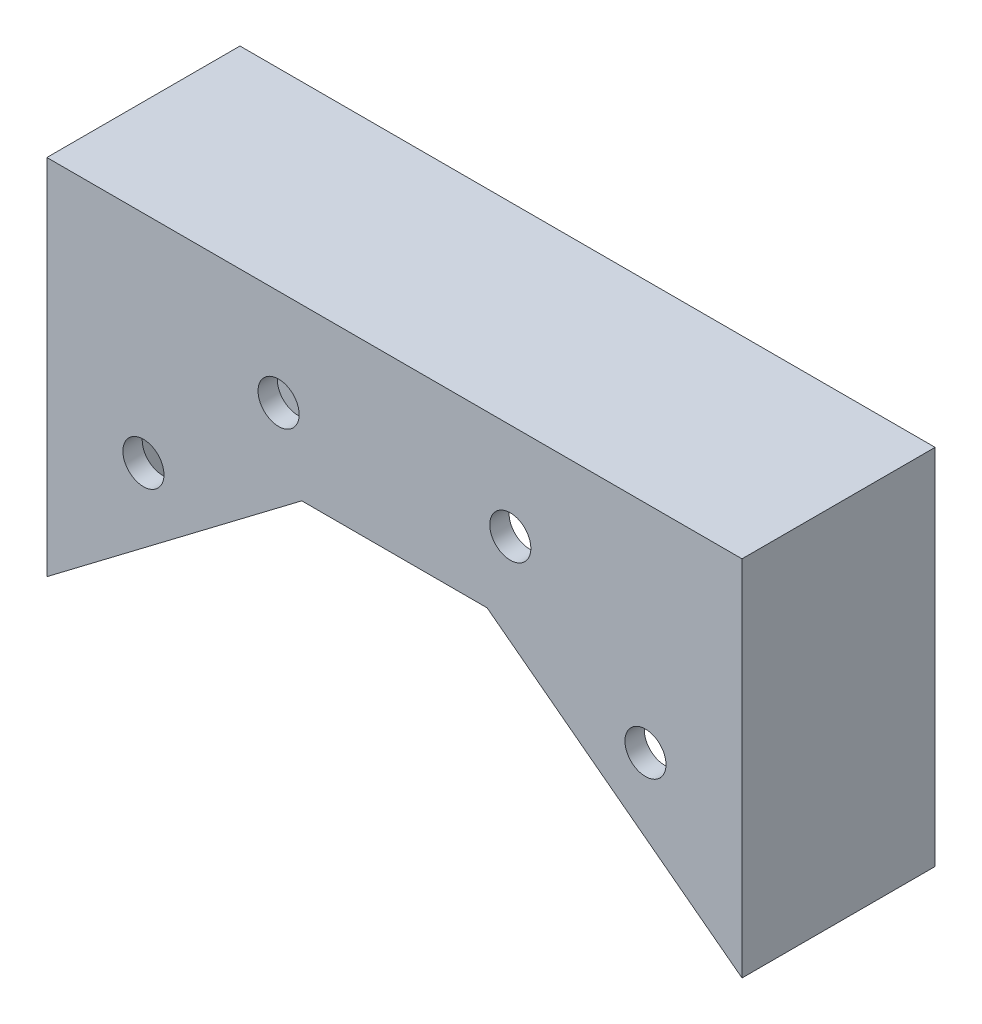
SolidWorks part; units mm, degrees
material "PPE"
ref_plane "Front Plane" through (0, 0, 0) normal (0, 0, 1) x (1, 0, 0)
ref_plane "Top Plane" through (0, 0, 0) normal (0, 1, 0) x (1, 0, 0)
ref_plane "Right Plane" through (0, 0, 0) normal (1, 0, 0) x (0, 0, -1)
sketch "Sketch2" plane through (0, 0, 0) normal (0, 0, 1) x (1, 0, 0)
  line L5 (0, 0) -> (0, 27.94) construction
  line L6 (-15.24, 0) -> (15.24, 0)
  line L9 (15.24, 0) -> (57.15, -31.75)
  line L13 (57.15, -31.75) -> (57.15, 27.94)
  line L14 (57.15, 27.94) -> (-57.15, 27.94)
  line L15 (-15.24, 0) -> (-57.15, -31.75)
  line L16 (-57.15, -31.75) -> (-57.15, 27.94)
  dimension "D1" = 27.94
  dimension "D2" = 114.3
  dimension "D3" = 31.75
  dimension "D4" = 15.24
extrude "Boss-Extrude2" add sketch "Sketch2" along normal mid plane 31.75
shell "Shell2" thickness 3.175
sketch "Sketch3" plane through (0, 0, -15.875) normal (0, 0, -1) x (-1, 0, 0)
  line L0 (41.275, 27.94) -> (41.275, -34.1369) construction
  line L1 (-57.15, 27.94) -> (57.15, 27.94) construction
  line L2 (0, 0) -> (0, 52.0779) construction
  line L3 (15.24, 0) -> (-15.24, 0) construction
  line L4 (57.15, 27.94) -> (57.15, -31.75) construction
  circle A0 centre (41.275, -7.62) radius 3.3782
  circle A1 centre (19.05, 12.065) radius 3.3782
  circle A5 centre (-19.05, 12.065) radius 3.3782
  circle A6 centre (-41.275, -7.62) radius 3.3782
  dimension "D4" = 6.7564
  dimension "D2" = 15.875
  dimension "D3" = 35.56
  dimension "D5" = 15.875
  dimension "D8" = 19.05
extrude "Cut-Extrude1" cut sketch "Sketch3" against normal through all
